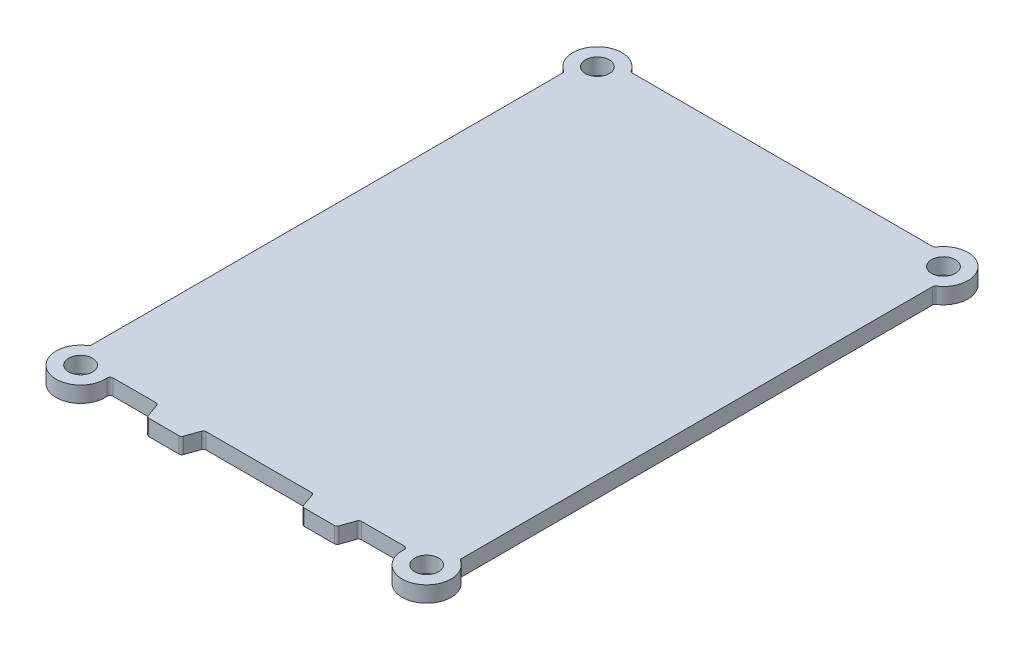
SolidWorks part; units mm, degrees
ref_plane "Front Plane" through (0, 0, 0) normal (0, 0, 1) x (1, 0, 0)
ref_plane "Top Plane" through (0, 0, 0) normal (0, 1, 0) x (1, 0, 0)
ref_plane "Right Plane" through (0, 0, 0) normal (1, 0, 0) x (0, 0, -1)
sketch "Sketch1" plane through (0, 0, 0) normal (0, 1, 0) x (1, 0, 0)
  line L0 (0, 83.2953) -> (0, 0)
  line L5 (65, 83.2953) -> (65, 0)
  line L6 (5.8523, 89.1477) -> (59.1477, 89.1477)
  line L7 (5.8523, -5.8523) -> (59.1477, -5.8523)
  line L8 (0, 41.6477) -> (65, 41.6477) construction
  line L9 (32.5, -5.8523) -> (32.5, 89.1477) construction
  circle A0 centre (2.1, 87.0477) radius 2.1
  arc A1 (5.8523, 89.1477) -> (0, 83.2953) centre (2.1, 87.0477) ccw
  arc A2 (5.8523, -5.8523) -> (0, 0) centre (2.1, -3.7523) cw
  circle A3 centre (2.1, -3.7523) radius 2.1
  arc A4 (59.1477, -5.8523) -> (65, 0) centre (62.9, -3.7523) ccw
  circle A5 centre (62.9, -3.7523) radius 2.1
  arc A6 (59.1477, 89.1477) -> (65, 83.2953) centre (62.9, 87.0477) cw
  circle A7 centre (62.9, 87.0477) radius 2.1
  dimension "D1" = 4.2
  dimension "D2" = 2.2
  dimension "D3" = 95
  dimension "D4" = 65
extrude "Boss-Extrude1" add sketch "Sketch1" along normal blind 2.8
sketch "Sketch2" plane through (0, 2.8, 0) normal (0, 1, 0) x (1, 0, 0)
  line L0 (32.5, -5.8523) -> (32.5, 89.1477) construction
  line L1 (5.8523, -5.8523) -> (59.1477, -5.8523) construction
  line L2 (59.1477, 89.1477) -> (5.8523, 89.1477) construction
  line L4 (22.9, -2.8523) -> (21.8524, -5.8523)
  line L5 (21.8524, -5.8523) -> (43.1476, -5.8523)
  line L6 (15.8524, -5.8523) -> (14.8048, -2.8523)
  line L7 (14.8048, -2.8523) -> (6.3048, -2.8523)
  line L8 (5.8523, -5.8523) -> (15.8524, -5.8523)
  line L11 (59.1477, -5.8523) -> (49.1476, -5.8523)
  line L12 (50.1952, -2.8523) -> (58.6952, -2.8523)
  line L13 (49.1476, -5.8523) -> (50.1952, -2.8523)
  line L14 (22.9, -2.8523) -> (42.1, -2.8523)
  line L15 (42.1, -2.8523) -> (43.1476, -5.8523)
  arc A0 (5.8523, -5.8523) -> (6.3048, -2.8523) centre (2.1, -3.7523) ccw
  arc A1 (59.1477, -5.8523) -> (58.6952, -2.8523) centre (62.9, -3.7523) cw
  dimension "D1" = 3
  dimension "D2" = 8.5
  dimension "D3" = 19.2
  dimension "D4" = 6
extrude "Cut-Extrude1" cut sketch "Sketch2" against normal up to next
fillet "Fillet1" radius 0.5 16 edges at (0, 1.4, -83.2953) (5.8523, 1.4, -89.1477) (59.1477, 1.4, -89.1477) (65, 1.4, -83.2953) (65, 1.4, 0) (0, 1.4, 0) (6.3048, 1.4, 2.8523) (14.8048, 1.4, 2.8523) (15.8524, 1.4, 5.8523) (21.8524, 1.4, 5.8523) (22.9, 1.4, 2.8523) (58.6952, 1.4, 2.8523) (42.1, 1.4, 2.8523) (43.1476, 1.4, 5.8523) (49.1476, 1.4, 5.8523) (50.1952, 1.4, 2.8523)
